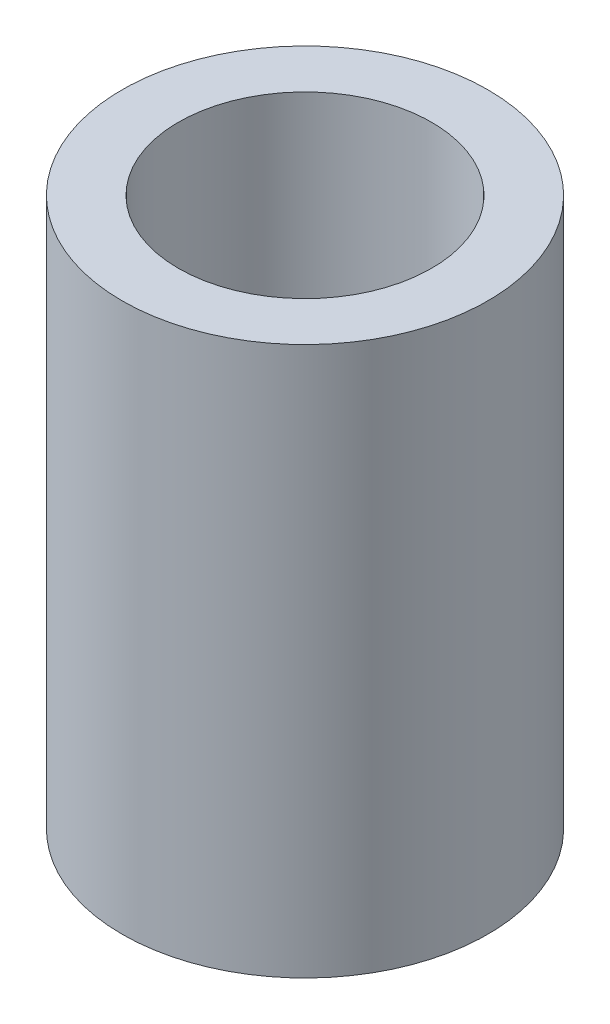
SolidWorks part; units mm, degrees
ref_plane "Alzado" through (0, 0, 0) normal (0, 0, 1) x (1, 0, 0)
ref_plane "Planta" through (0, 0, 0) normal (0, 1, 0) x (1, 0, 0)
ref_plane "Vista lateral" through (0, 0, 0) normal (1, 0, 0) x (0, 0, -1)
sketch "Croquis1" plane through (0, 0, 0) normal (0, 1, 0) x (1, 0, 0)
  circle A0 centre (0, 0) radius 4.5
  circle A1 centre (0, 0) radius 6.5
  dimension "D1" = 9
  dimension "D2" = 2
extrude "Saliente-Extruir1" add sketch "Croquis1" along normal blind 19.5
